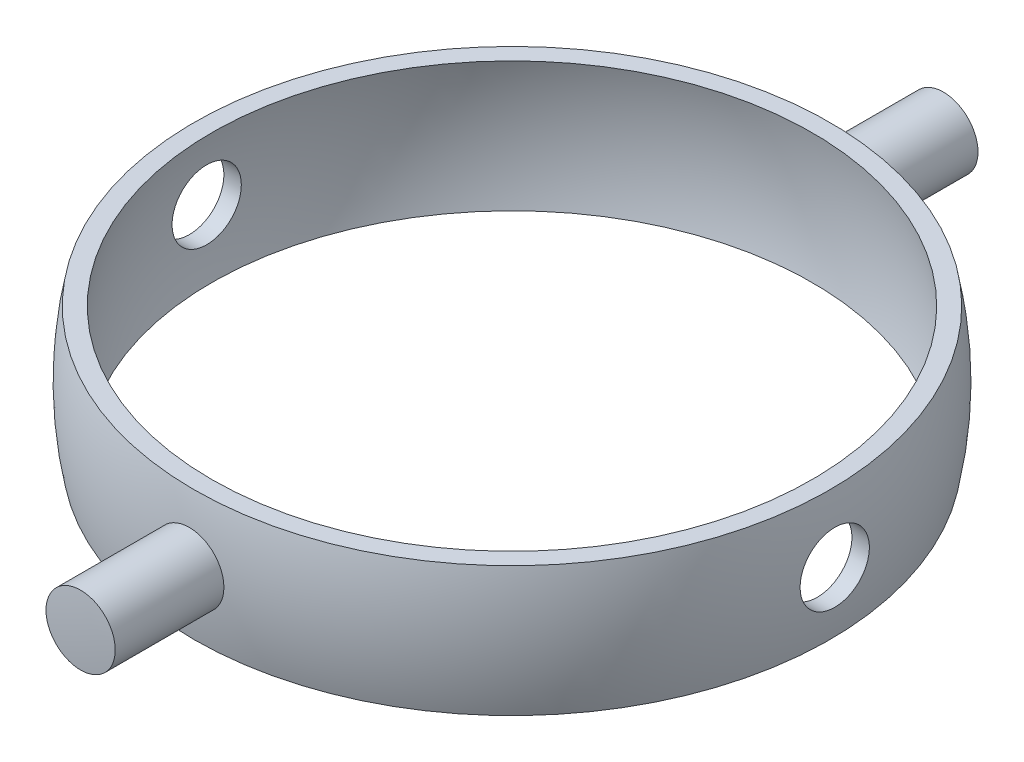
SolidWorks part; units mm, degrees
ref_plane "Front Plane" through (0, 0, 0) normal (0, 0, 1) x (1, 0, 0)
ref_plane "Top Plane" through (0, 0, 0) normal (0, 1, 0) x (1, 0, 0)
ref_plane "Right Plane" through (0, 0, 0) normal (1, 0, 0) x (0, 0, -1)
sketch "Sketch1" plane through (0, 0, 0) normal (0, 0, 1) x (1, 0, 0)
  line L0 (0, 20.3735) -> (0, 0) construction
  line L1 (0, 0) -> (-36.8948, 0) construction
  line L4 (-36.7423, 7.5) -> (-34.6987, 7.5)
  line L5 (-36.7423, -7.5) -> (-34.6987, -7.5)
  arc A0 (-34.6987, 7.5) -> (-34.6987, -7.5) centre (0, 0) ccw
  arc A1 (-36.7423, 7.5) -> (-36.7423, -7.5) centre (0, 0) ccw
  dimension "D1" = 37.5
  dimension "D2" = 35.5
  dimension "D3" = 15
revolve "Revolve1" add sketch "Sketch1" angle 360 about L0
sketch "Sketch2" plane through (0, 0, 0) normal (1, 0, 0) x (0, 0, -1)
  line L0 (0, 7.5) -> (0, 0) construction
  line L1 (36.7423, 7.5) -> (-36.7423, 7.5) construction
  circle A0 centre (0, 0) radius 4
  dimension "D1" = 8
extrude "Cut-Extrude1" cut sketch "Sketch2" against normal through all both and the other way through all
ref_plane "Plane1" through (0, 0, 50) normal (0, 0, 1) x (1, 0, 0)
sketch "Sketch3" plane through (0, 0, 50) normal (0, 0, 1) x (1, 0, 0)
  circle A0 centre (0, 0) radius 4
  dimension "D1" = 8
extrude "Boss-Extrude1" add sketch "Sketch3" against normal up to surface (12.7139 mm away)
mirror "Mirror1" about plane through (0, 0, 0) normal (0, 0, 1) of "Boss-Extrude1"
sketch "Sketch4" plane through (0, 0, 0) normal (1, 0, 0) x (0, 0, -1)
  line L0 (0, 37.66) -> (0, 0) construction
  line L1 (0, 0) -> (-50, 0) construction
  line L2 (-50, 4) -> (-50, -4) construction
  line L3 (0, -50) -> (0, -55)
  line L4 (0, 55) -> (0, 50)
  arc A0 (0, 50) -> (0, -50) centre (0, 0) ccw
  arc A1 (0, 55) -> (0, -55) centre (0, 0) ccw
  point P10 (0, 0)
  dimension "D1" = 55
  dimension "D2" = 50
revolve "Cut-Revolve1" cut sketch "Sketch4" angle 360 about L0
